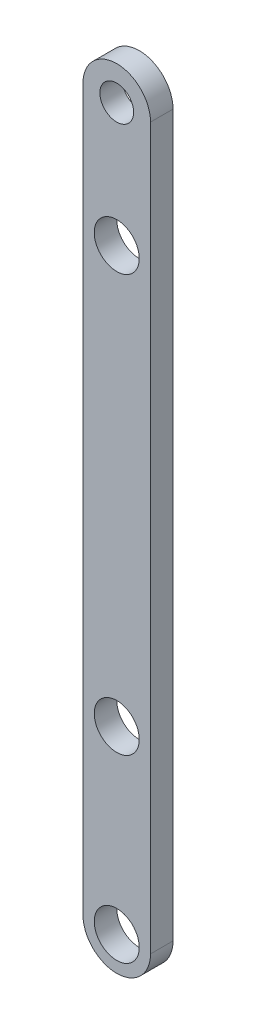
SolidWorks part; units mm, degrees
ref_plane "Front Plane" through (0, 0, 0) normal (0, 0, 1) x (1, 0, 0)
ref_plane "Top Plane" through (0, 0, 0) normal (0, 1, 0) x (1, 0, 0)
ref_plane "Right Plane" through (0, 0, 0) normal (1, 0, 0) x (0, 0, -1)
sketch "Sketch1" plane through (0, 0, 0) normal (0, 0, 1) x (1, 0, 0)
  line L0 (0, 16) -> (0, -16) construction
  line L1 (1.5, 16) -> (1.5, -16)
  line L2 (-1.5, 16) -> (-1.5, -16)
  arc A0 (1.5, 16) -> (-1.5, 16) centre (0, 16) ccw
  arc A1 (-1.5, -16) -> (1.5, -16) centre (0, -16) ccw
  circle A2 centre (0, 16) radius 0.75
  circle A3 centre (0, -16) radius 1
  circle A4 centre (0, 10.5) radius 1
  circle A5 centre (0, -8) radius 1
  point P2 (0, 0)
  dimension "D1" = 1.5
  dimension "D2" = 1.5
  dimension "D5" = 1.5
  dimension "D6" = 32
  dimension "D8" = 2
  dimension "D9" = 2
  dimension "D10" = 2
  dimension "D3" = 5.5
  dimension "D4" = 8
  dimension "D7" = 10.5
extrude "Boss-Extrude1" add sketch "Sketch1" along normal blind 1
